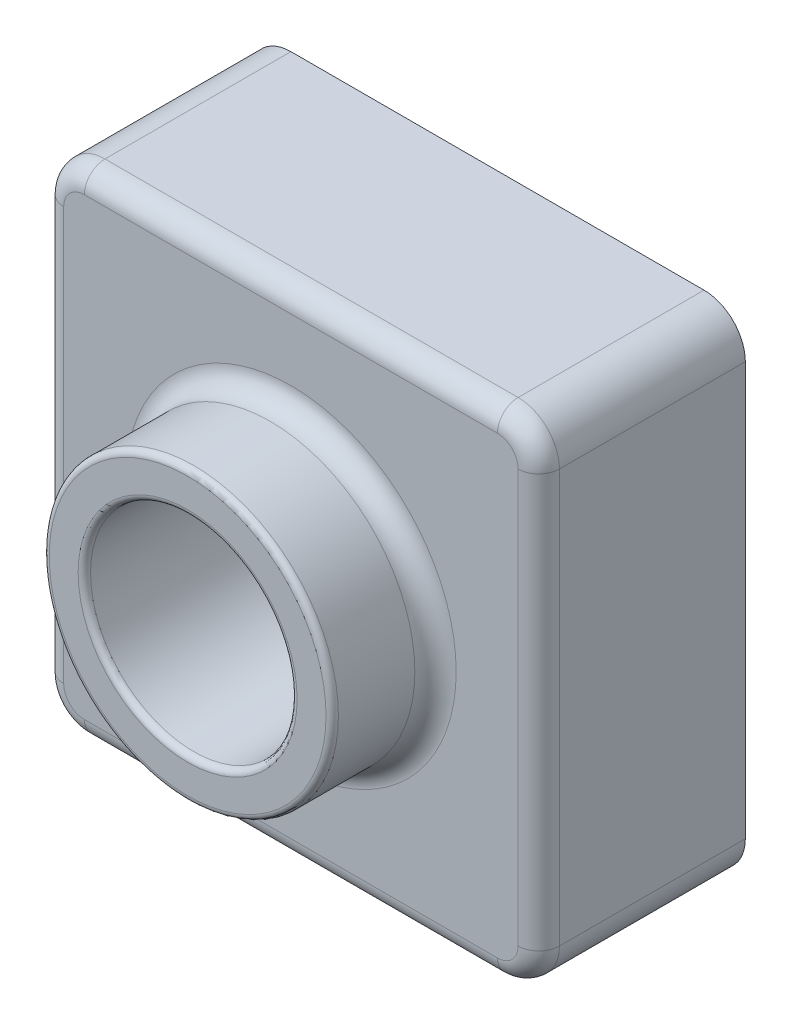
SolidWorks part; units mm, degrees
material "Chrome Stainless Steel"
ref_plane "Front Plane" through (0, 0, 0) normal (0, 0, 1) x (1, 0, 0)
ref_plane "Top Plane" through (0, 0, 0) normal (0, 1, 0) x (1, 0, 0)
ref_plane "Right Plane" through (0, 0, 0) normal (1, 0, 0) x (0, 0, -1)
sketch "Sketch1" plane through (0, 0, 0) normal (0, 0, 1) x (1, 0, 0)
  line L1 (-60, -60) -> (60, -60)
  line L2 (-60, -60) -> (-60, 60)
  line L3 (-60, 60) -> (60, 60)
  line L4 (60, -60) -> (60, 60)
  line L5 (-60, -60) -> (60, 60) construction
  line L6 (-60, 60) -> (60, -60) construction
  point P0 (0, 0)
  dimension "D1" = 120
  dimension "D2" = 120
extrude "Boss-Extrude2" add sketch "Sketch1" along normal blind 50 contours L2 L1 L4 L3
sketch "Sketch2" plane through (0, 0, 50) normal (0, 0, 1) x (1, 0, 0)
  line L1 (-60, -60) -> (-60, 60) construction
  line L3 (-60, 60) -> (60, 60) construction
  circle A0 centre (0, 0) radius 35
  dimension "D1" = 70
  dimension "D2" = 60
  dimension "D3" = 60
extrude "Boss-Extrude3" add sketch "Sketch2" along normal blind 25
sketch "Sketch3" plane through (0, 0, 75) normal (0, 0, 1) x (1, 0, 0)
  circle A0 centre (0, 0) radius 25
  dimension "D1" = 50
extrude "Cut-Extrude1" cut sketch "Sketch3" against normal blind 55
fillet "Fillet1" radius 10 4 edges at (-60, 60, 25) (60, 60, 25) (60, -60, 25) (-60, -60, 25)
fillet "Fillet2" radius 1.5 2 edges at (35, 0, 75) (25, 0, 75)
fillet "Fillet3" radius 5 9 edges at (57.0711, 57.0711, 50) (60, 0, 50) (57.0711, -57.0711, 50) (0, -60, 50) (-57.0711, -57.0711, 50) (-60, 0, 50) (-57.0711, 57.0711, 50) (0, 60, 50) (35, 0, 50)
shell "Shell1" thickness 2
